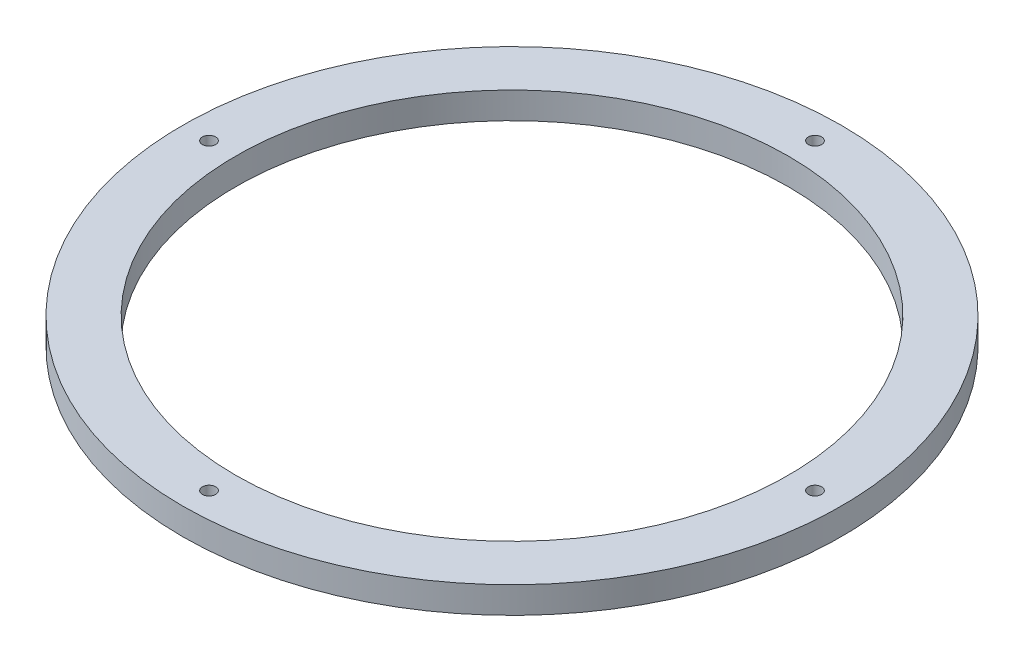
SolidWorks part; units mm, degrees
ref_plane "Front Plane" through (0, 0, 0) normal (0, 0, 1) x (1, 0, 0)
ref_plane "Top Plane" through (0, 0, 0) normal (0, 1, 0) x (1, 0, 0)
ref_plane "Right Plane" through (0, 0, 0) normal (1, 0, 0) x (0, 0, -1)
sketch "Sketch1" plane through (0, 0, 0) normal (0, 1, 0) x (1, 0, 0)
  line L0 (0, 0) -> (36.195, 0) construction
  line L1 (0, 0) -> (36.195, 0) construction
  circle A0 centre (0, 0) radius 33.02
  circle A1 centre (0, 0) radius 39.37
  circle A2 centre (36.195, 0) radius 0.7937
  circle A3 centre (0, -36.195) radius 0.7937
  circle A4 centre (-36.195, 0) radius 0.7937
  circle A5 centre (0, 36.195) radius 0.7937
  dimension "D1" = 66.04
  dimension "D2" = 78.74
  dimension "D4" = 1.5875
  dimension "D3" = 36.195
  dimension "D6" = 36.195
  dimension "D5" = 4
extrude "Boss-Extrude1" add sketch "Sketch1" along normal blind 3.175
